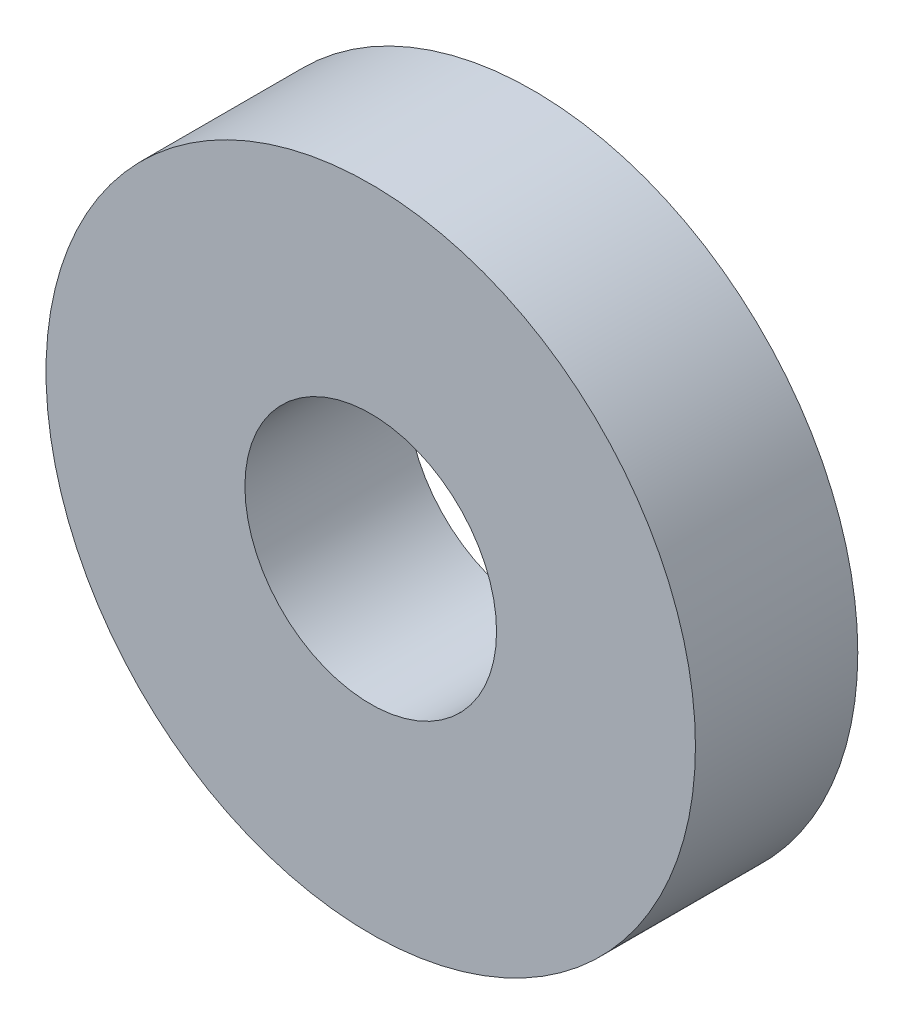
SolidWorks part; units mm, degrees
material "ABS"
ref_plane "Front Plane" through (0, 0, 0) normal (0, 0, 1) x (1, 0, 0)
ref_plane "Top Plane" through (0, 0, 0) normal (0, 1, 0) x (1, 0, 0)
ref_plane "Right Plane" through (0, 0, 0) normal (1, 0, 0) x (0, 0, -1)
sketch "Sketch1" plane through (0, 0, 0) normal (0, 0, 1) x (1, 0, 0)
  circle A0 centre (0, 0) radius 4
  dimension "D1" = 8
extrude "Boss-Extrude1" add sketch "Sketch1" along normal blind 2
hole_wizard "M2.5 Clearance Hole1" positions "Sketch2" profile "Sketch3" hole size "M2.5" standard "ANSI Metric" end condition through all
sketch "Sketch2" plane through (0, 0, 2) normal (0, 0, 1) x (1, 0, 0)
  point P0 (0, 0)
sketch "Sketch3" plane through (0, 0, 2) normal (1, 0, 0) x (0, -1, 0)
  line L0 (0, 0) -> (0, 2)
  line L1 (0, 2) -> (1.55, 2)
  line L2 (1.55, 2) -> (1.55, 0)
  line L5 (1.55, 0) -> (0, 0)
  line L11 (0, -6.35) -> (0, 107.95) construction
  dimension "Thru Hole Dia." = 3.1
  dimension "Thru Hole Depth" = 2
